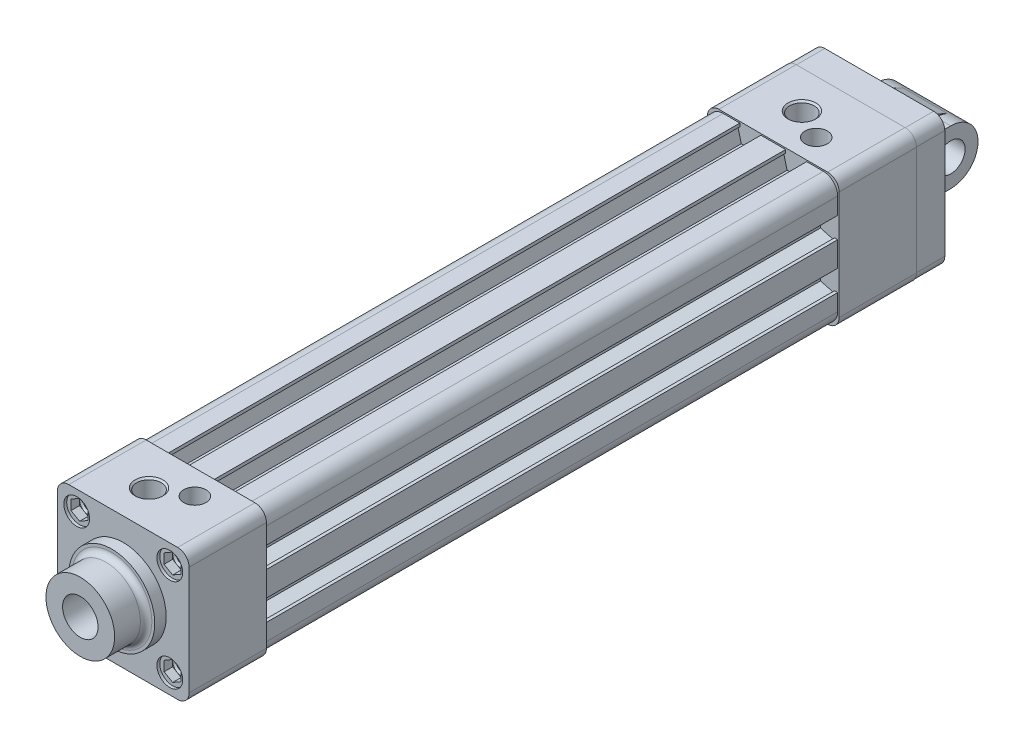
SolidWorks part; units mm, degrees
ref_plane "Front Plane" through (0, 0, 0) normal (0, 0, 1) x (1, 0, 0)
ref_plane "Top Plane" through (0, 0, 0) normal (0, 1, 0) x (1, 0, 0)
ref_plane "Right Plane" through (0, 0, 0) normal (1, 0, 0) x (0, 0, -1)
ref_plane "Plane1" through (0, 0, -254) normal (0, 0, 1) x (1, 0, 0)
sketch "Sketch1" plane through (0, 0, -254) normal (0, 0, 1) x (1, 0, 0)
  line L0 (-19, -23) -> (19, -23)
  line L1 (23, -19) -> (23, 19)
  line L2 (19, 23) -> (-19, 23)
  line L3 (-23, 19) -> (-23, -19)
  arc A0 (-23, -19) -> (-19, -23) centre (-19, -19) ccw
  arc A1 (19, -23) -> (23, -19) centre (19, -19) ccw
  arc A2 (23, 19) -> (19, 23) centre (19, 19) ccw
  arc A3 (-19, 23) -> (-23, 19) centre (-19, 19) ccw
extrude "Boss-Extrude1" add sketch "Sketch1" along normal blind 27
ref_plane "Plane2" through (0, 0, -227) normal (0, 0, 1) x (1, 0, 0)
sketch "Sketch2" plane through (0, 0, -227) normal (0, 0, 1) x (1, 0, 0)
  line L0 (-17.5, -22.5) -> (-11.675, -22.5)
  line L1 (-11.675, -22.5) -> (-11.675, -21.393)
  line L2 (-11.675, -21.393) -> (-12.3558, -21)
  line L3 (-12.3558, -21) -> (-11.15, -16.5)
  line L4 (-11.15, -16.5) -> (-4.85, -16.5)
  line L5 (-4.85, -16.5) -> (-3.6442, -21)
  line L6 (-3.6442, -21) -> (-4.325, -21.393)
  line L7 (-4.325, -21.393) -> (-4.325, -22.5)
  line L8 (-4.325, -22.5) -> (4.325, -22.5)
  line L9 (4.325, -22.5) -> (4.325, -21.393)
  line L10 (4.325, -21.393) -> (3.6442, -21)
  line L11 (3.6442, -21) -> (4.85, -16.5)
  line L12 (4.85, -16.5) -> (11.15, -16.5)
  line L13 (11.15, -16.5) -> (12.3558, -21)
  line L14 (12.3558, -21) -> (11.675, -21.393)
  line L15 (11.675, -21.393) -> (11.675, -22.5)
  line L16 (11.675, -22.5) -> (17.5, -22.5)
  line L17 (22.5, -17.5) -> (22.5, -11.675)
  line L18 (22.5, -11.675) -> (21.393, -11.675)
  line L19 (21.393, -11.675) -> (21, -12.3558)
  line L20 (21, -12.3558) -> (16.5, -11.15)
  line L21 (16.5, -11.15) -> (16.5, -4.85)
  line L22 (16.5, -4.85) -> (21, -3.6442)
  line L23 (21, -3.6442) -> (21.393, -4.325)
  line L24 (21.393, -4.325) -> (22.5, -4.325)
  line L25 (22.5, -4.325) -> (22.5, 4.325)
  line L26 (22.5, 4.325) -> (21.393, 4.325)
  line L27 (21.393, 4.325) -> (21, 3.6442)
  line L28 (21, 3.6442) -> (16.5, 4.85)
  line L29 (16.5, 4.85) -> (16.5, 11.15)
  line L30 (16.5, 11.15) -> (21, 12.3558)
  line L31 (21, 12.3558) -> (21.393, 11.675)
  line L32 (21.393, 11.675) -> (22.5, 11.675)
  line L33 (22.5, 11.675) -> (22.5, 17.5)
  line L34 (17.5, 22.5) -> (11.675, 22.5)
  line L35 (11.675, 22.5) -> (11.675, 21.393)
  line L36 (11.675, 21.393) -> (12.3558, 21)
  line L37 (12.3558, 21) -> (11.15, 16.5)
  line L38 (11.15, 16.5) -> (4.85, 16.5)
  line L39 (4.85, 16.5) -> (3.6442, 21)
  line L40 (3.6442, 21) -> (4.325, 21.393)
  line L41 (4.325, 21.393) -> (4.325, 22.5)
  line L42 (4.325, 22.5) -> (-4.325, 22.5)
  line L43 (-4.325, 22.5) -> (-4.325, 21.393)
  line L44 (-4.325, 21.393) -> (-3.6442, 21)
  line L45 (-3.6442, 21) -> (-4.85, 16.5)
  line L46 (-4.85, 16.5) -> (-11.15, 16.5)
  line L47 (-11.15, 16.5) -> (-12.3558, 21)
  line L48 (-12.3558, 21) -> (-11.675, 21.393)
  line L49 (-11.675, 21.393) -> (-11.675, 22.5)
  line L50 (-11.675, 22.5) -> (-17.5, 22.5)
  line L51 (-22.5, 17.5) -> (-22.5, 11.675)
  line L52 (-22.5, 11.675) -> (-21.393, 11.675)
  line L53 (-21.393, 11.675) -> (-21, 12.3558)
  line L54 (-21, 12.3558) -> (-16.5, 11.15)
  line L55 (-16.5, 11.15) -> (-16.5, 4.85)
  line L56 (-16.5, 4.85) -> (-21, 3.6442)
  line L57 (-21, 3.6442) -> (-21.393, 4.325)
  line L58 (-21.393, 4.325) -> (-22.5, 4.325)
  line L59 (-22.5, 4.325) -> (-22.5, -4.325)
  line L60 (-22.5, -4.325) -> (-21.393, -4.325)
  line L61 (-21.393, -4.325) -> (-21, -3.6442)
  line L62 (-21, -3.6442) -> (-16.5, -4.85)
  line L63 (-16.5, -4.85) -> (-16.5, -11.15)
  line L64 (-16.5, -11.15) -> (-21, -12.3558)
  line L65 (-21, -12.3558) -> (-21.393, -11.675)
  line L66 (-21.393, -11.675) -> (-22.5, -11.675)
  line L67 (-22.5, -11.675) -> (-22.5, -17.5)
  arc A0 (-22.5, -17.5) -> (-17.5, -22.5) centre (-17.5, -17.5) ccw
  arc A1 (17.5, -22.5) -> (22.5, -17.5) centre (17.5, -17.5) ccw
  arc A2 (22.5, 17.5) -> (17.5, 22.5) centre (17.5, 17.5) ccw
  arc A3 (-17.5, 22.5) -> (-22.5, 17.5) centre (-17.5, 17.5) ccw
extrude "Boss-Extrude2" add sketch "Sketch2" along normal blind 200
ref_plane "Plane3" through (0, 0, 0) normal (0, 0, 1) x (1, 0, 0)
sketch "Sketch3" plane through (0, 0, 0) normal (0, 0, 1) x (1, 0, 0)
  line L0 (-19, -23) -> (19, -23)
  line L1 (23, -19) -> (23, 19)
  line L2 (19, 23) -> (-19, 23)
  line L3 (-23, 19) -> (-23, -19)
  arc A0 (-23, -19) -> (-19, -23) centre (-19, -19) ccw
  arc A1 (19, -23) -> (23, -19) centre (19, -19) ccw
  arc A2 (23, 19) -> (19, 23) centre (19, 19) ccw
  arc A3 (-19, 23) -> (-23, 19) centre (-19, 19) ccw
extrude "Boss-Extrude3" add sketch "Sketch3" against normal blind 27
ref_plane "Plane4" through (0, 0, 0) normal (0, 0, 1) x (1, 0, 0)
sketch "Sketch4" plane through (0, 0, 0) normal (0, 0, 1) x (1, 0, 0)
  line L0 (13.25, 17.9821) -> (13.25, 14.5179)
  line L1 (13.25, 14.5179) -> (16.25, 12.7859)
  line L2 (16.25, 12.7859) -> (19.25, 14.5179)
  line L3 (19.25, 14.5179) -> (19.25, 17.9821)
  line L4 (19.25, 17.9821) -> (16.25, 19.7141)
  line L5 (16.25, 19.7141) -> (13.25, 17.9821)
extrude "Cut-Extrude1" cut sketch "Sketch4" against normal blind 4
ref_plane "Plane5" through (16.25, 0, 0) normal (1, 0, 0) x (0, 0, -1)
sketch "Sketch5" plane through (16.25, 0, 0) normal (1, 0, 0) x (0, 0, -1)
  line L0 (17, 16.25) -> (17, 13.8635)
  line L1 (17, 13.8635) -> (4.6135, 13.8635)
  line L2 (4.6135, 13.8635) -> (4, 13.25)
  line L3 (4, 13.25) -> (1, 13.25)
  line L4 (1, 13.25) -> (1, 11.75)
  line L5 (1, 11.75) -> (-1, 11.75)
  line L6 (-1, 11.75) -> (-1, 16.25)
  line L7 (-1, 16.25) -> (17, 16.25)
  line L8 (-1, 16.25) -> (17, 16.25) construction
revolve "Cut-Revolve1" cut sketch "Sketch5" angle 360 about L8
cosmetic thread "Cosmetic Thread1" parameters "D1"=12.3865, "D2"=6
ref_plane "Plane6" through (0, 0, 0) normal (0, 0, 1) x (1, 0, 0)
sketch "Sketch6" plane through (0, 0, 0) normal (0, 0, 1) x (1, 0, 0)
  line L0 (-19.25, 17.9821) -> (-19.25, 14.5179)
  line L1 (-19.25, 14.5179) -> (-16.25, 12.7859)
  line L2 (-16.25, 12.7859) -> (-13.25, 14.5179)
  line L3 (-13.25, 14.5179) -> (-13.25, 17.9821)
  line L4 (-13.25, 17.9821) -> (-16.25, 19.7141)
  line L5 (-16.25, 19.7141) -> (-19.25, 17.9821)
extrude "Cut-Extrude2" cut sketch "Sketch6" against normal blind 4
ref_plane "Plane7" through (-16.25, 0, 0) normal (1, 0, 0) x (0, 0, -1)
sketch "Sketch7" plane through (-16.25, 0, 0) normal (1, 0, 0) x (0, 0, -1)
  line L0 (17, 16.25) -> (17, 13.8635)
  line L1 (17, 13.8635) -> (4.6135, 13.8635)
  line L2 (4.6135, 13.8635) -> (4, 13.25)
  line L3 (4, 13.25) -> (1, 13.25)
  line L4 (1, 13.25) -> (1, 11.75)
  line L5 (1, 11.75) -> (-1, 11.75)
  line L6 (-1, 11.75) -> (-1, 16.25)
  line L7 (-1, 16.25) -> (17, 16.25)
  line L8 (-1, 16.25) -> (17, 16.25) construction
revolve "Cut-Revolve2" cut sketch "Sketch7" angle 360 about L8
cosmetic thread "Cosmetic Thread2" parameters "D1"=12.3865, "D2"=6
ref_plane "Plane8" through (0, 0, 0) normal (0, 0, 1) x (1, 0, 0)
sketch "Sketch8" plane through (0, 0, 0) normal (0, 0, 1) x (1, 0, 0)
  line L0 (-19.25, -17.9821) -> (-16.25, -19.7141)
  line L1 (-16.25, -19.7141) -> (-13.25, -17.9821)
  line L2 (-13.25, -17.9821) -> (-13.25, -14.5179)
  line L3 (-13.25, -14.5179) -> (-16.25, -12.7859)
  line L4 (-16.25, -12.7859) -> (-19.25, -14.5179)
  line L5 (-19.25, -14.5179) -> (-19.25, -17.9821)
extrude "Cut-Extrude3" cut sketch "Sketch8" against normal blind 4
ref_plane "Plane9" through (-16.25, 0, 0) normal (1, 0, 0) x (0, 0, -1)
sketch "Sketch9" plane through (-16.25, 0, 0) normal (1, 0, 0) x (0, 0, -1)
  line L0 (-1, -16.25) -> (-1, -11.75)
  line L1 (-1, -11.75) -> (1, -11.75)
  line L2 (1, -11.75) -> (1, -13.25)
  line L3 (1, -13.25) -> (4, -13.25)
  line L4 (4, -13.25) -> (4.6135, -13.8635)
  line L5 (4.6135, -13.8635) -> (17, -13.8635)
  line L6 (17, -13.8635) -> (17, -16.25)
  line L7 (17, -16.25) -> (-1, -16.25)
  line L8 (17, -16.25) -> (-1, -16.25) construction
revolve "Cut-Revolve3" cut sketch "Sketch9" angle 360 about L8
cosmetic thread "Cosmetic Thread3" parameters "D1"=12.3865, "D2"=6
ref_plane "Plane10" through (0, 0, 0) normal (0, 0, 1) x (1, 0, 0)
sketch "Sketch10" plane through (0, 0, 0) normal (0, 0, 1) x (1, 0, 0)
  line L0 (13.25, -14.5179) -> (13.25, -17.9821)
  line L1 (13.25, -17.9821) -> (16.25, -19.7141)
  line L2 (16.25, -19.7141) -> (19.25, -17.9821)
  line L3 (19.25, -17.9821) -> (19.25, -14.5179)
  line L4 (19.25, -14.5179) -> (16.25, -12.7859)
  line L5 (16.25, -12.7859) -> (13.25, -14.5179)
extrude "Cut-Extrude4" cut sketch "Sketch10" against normal blind 4
ref_plane "Plane11" through (16.25, 0, 0) normal (1, 0, 0) x (0, 0, -1)
sketch "Sketch11" plane through (16.25, 0, 0) normal (1, 0, 0) x (0, 0, -1)
  line L0 (-1, -16.25) -> (-1, -11.75)
  line L1 (-1, -11.75) -> (1, -11.75)
  line L2 (1, -11.75) -> (1, -13.25)
  line L3 (1, -13.25) -> (4, -13.25)
  line L4 (4, -13.25) -> (4.6135, -13.8635)
  line L5 (4.6135, -13.8635) -> (17, -13.8635)
  line L6 (17, -13.8635) -> (17, -16.25)
  line L7 (17, -16.25) -> (-1, -16.25)
  line L8 (17, -16.25) -> (-1, -16.25) construction
revolve "Cut-Revolve4" cut sketch "Sketch11" angle 360 about L8
cosmetic thread "Cosmetic Thread4" parameters "D1"=12.3865, "D2"=6
ref_plane "Plane12" through (0, 0, -254) normal (0, 0, 1) x (1, 0, 0)
sketch "Sketch12" plane through (0, 0, -254) normal (0, 0, 1) x (1, 0, 0)
  line L0 (13.25, 17.9821) -> (13.25, 14.5179)
  line L1 (13.25, 14.5179) -> (16.25, 12.7859)
  line L2 (16.25, 12.7859) -> (19.25, 14.5179)
  line L3 (19.25, 14.5179) -> (19.25, 17.9821)
  line L4 (19.25, 17.9821) -> (16.25, 19.7141)
  line L5 (16.25, 19.7141) -> (13.25, 17.9821)
extrude "Cut-Extrude5" cut sketch "Sketch12" along normal blind 4
ref_plane "Plane13" through (16.25, 0, 0) normal (1, 0, 0) x (0, 0, -1)
sketch "Sketch13" plane through (16.25, 0, 0) normal (1, 0, 0) x (0, 0, -1)
  line L0 (255, 16.25) -> (255, 11.75)
  line L1 (255, 11.75) -> (253, 11.75)
  line L2 (253, 11.75) -> (253, 13.25)
  line L3 (253, 13.25) -> (250, 13.25)
  line L4 (250, 13.25) -> (249.3865, 13.8635)
  line L5 (249.3865, 13.8635) -> (237, 13.8635)
  line L6 (237, 13.8635) -> (237, 16.25)
  line L7 (237, 16.25) -> (255, 16.25)
  line L8 (237, 16.25) -> (255, 16.25) construction
revolve "Cut-Revolve5" cut sketch "Sketch13" angle 360 about L8
cosmetic thread "Cosmetic Thread5" parameters "D1"=12.3865, "D2"=6
ref_plane "Plane14" through (0, 0, -254) normal (0, 0, 1) x (1, 0, 0)
sketch "Sketch14" plane through (0, 0, -254) normal (0, 0, 1) x (1, 0, 0)
  line L0 (-19.25, 17.9821) -> (-19.25, 14.5179)
  line L1 (-19.25, 14.5179) -> (-16.25, 12.7859)
  line L2 (-16.25, 12.7859) -> (-13.25, 14.5179)
  line L3 (-13.25, 14.5179) -> (-13.25, 17.9821)
  line L4 (-13.25, 17.9821) -> (-16.25, 19.7141)
  line L5 (-16.25, 19.7141) -> (-19.25, 17.9821)
extrude "Cut-Extrude6" cut sketch "Sketch14" along normal blind 4
ref_plane "Plane15" through (-16.25, 0, 0) normal (1, 0, 0) x (0, 0, -1)
sketch "Sketch15" plane through (-16.25, 0, 0) normal (1, 0, 0) x (0, 0, -1)
  line L0 (255, 16.25) -> (255, 11.75)
  line L1 (255, 11.75) -> (253, 11.75)
  line L2 (253, 11.75) -> (253, 13.25)
  line L3 (253, 13.25) -> (250, 13.25)
  line L4 (250, 13.25) -> (249.3865, 13.8635)
  line L5 (249.3865, 13.8635) -> (237, 13.8635)
  line L6 (237, 13.8635) -> (237, 16.25)
  line L7 (237, 16.25) -> (255, 16.25)
  line L8 (237, 16.25) -> (255, 16.25) construction
revolve "Cut-Revolve6" cut sketch "Sketch15" angle 360 about L8
cosmetic thread "Cosmetic Thread6" parameters "D1"=12.3865, "D2"=6
ref_plane "Plane16" through (0, 0, -254) normal (0, 0, 1) x (1, 0, 0)
sketch "Sketch16" plane through (0, 0, -254) normal (0, 0, 1) x (1, 0, 0)
  line L0 (13.25, -14.5179) -> (13.25, -17.9821)
  line L1 (13.25, -17.9821) -> (16.25, -19.7141)
  line L2 (16.25, -19.7141) -> (19.25, -17.9821)
  line L3 (19.25, -17.9821) -> (19.25, -14.5179)
  line L4 (19.25, -14.5179) -> (16.25, -12.7859)
  line L5 (16.25, -12.7859) -> (13.25, -14.5179)
extrude "Cut-Extrude7" cut sketch "Sketch16" along normal blind 4
ref_plane "Plane17" through (16.25, 0, 0) normal (1, 0, 0) x (0, 0, -1)
sketch "Sketch17" plane through (16.25, 0, 0) normal (1, 0, 0) x (0, 0, -1)
  line L0 (237, -16.25) -> (237, -13.8635)
  line L1 (237, -13.8635) -> (249.3865, -13.8635)
  line L2 (249.3865, -13.8635) -> (250, -13.25)
  line L3 (250, -13.25) -> (253, -13.25)
  line L4 (253, -13.25) -> (253, -11.75)
  line L5 (253, -11.75) -> (255, -11.75)
  line L6 (255, -11.75) -> (255, -16.25)
  line L7 (255, -16.25) -> (237, -16.25)
  line L8 (255, -16.25) -> (237, -16.25) construction
revolve "Cut-Revolve7" cut sketch "Sketch17" angle 360 about L8
cosmetic thread "Cosmetic Thread7" parameters "D1"=12.3865, "D2"=6
ref_plane "Plane18" through (0, 0, -254) normal (0, 0, 1) x (1, 0, 0)
sketch "Sketch18" plane through (0, 0, -254) normal (0, 0, 1) x (1, 0, 0)
  line L0 (-19.25, -14.5179) -> (-19.25, -17.9821)
  line L1 (-19.25, -17.9821) -> (-16.25, -19.7141)
  line L2 (-16.25, -19.7141) -> (-13.25, -17.9821)
  line L3 (-13.25, -17.9821) -> (-13.25, -14.5179)
  line L4 (-13.25, -14.5179) -> (-16.25, -12.7859)
  line L5 (-16.25, -12.7859) -> (-19.25, -14.5179)
extrude "Cut-Extrude8" cut sketch "Sketch18" along normal blind 4
ref_plane "Plane19" through (-16.25, 0, 0) normal (1, 0, 0) x (0, 0, -1)
sketch "Sketch19" plane through (-16.25, 0, 0) normal (1, 0, 0) x (0, 0, -1)
  line L0 (237, -16.25) -> (237, -13.8635)
  line L1 (237, -13.8635) -> (249.3865, -13.8635)
  line L2 (249.3865, -13.8635) -> (250, -13.25)
  line L3 (250, -13.25) -> (253, -13.25)
  line L4 (253, -13.25) -> (253, -11.75)
  line L5 (253, -11.75) -> (255, -11.75)
  line L6 (255, -11.75) -> (255, -16.25)
  line L7 (255, -16.25) -> (237, -16.25)
  line L8 (255, -16.25) -> (237, -16.25) construction
revolve "Cut-Revolve8" cut sketch "Sketch19" angle 360 about L8
cosmetic thread "Cosmetic Thread8" parameters "D1"=12.3865, "D2"=6
ref_plane "Plane20" through (-4, 0, 0) normal (1, 0, 0) x (0, 0, -1)
sketch "Sketch20" plane through (-4, 0, 0) normal (1, 0, 0) x (0, 0, -1)
  line L0 (13, 23) -> (17.864, 23)
  line L1 (17.864, 23) -> (17.283, 22.419)
  line L2 (17.283, 22.419) -> (17.283, 10.2928)
  line L3 (17.283, 10.2928) -> (13, 7.82)
  line L4 (13, 7.82) -> (13, 23)
  line L5 (13, -50) -> (13, 23) construction
revolve "Cut-Revolve9" cut sketch "Sketch20" angle 360 about L5
cosmetic thread "Cosmetic Thread9" parameters "D1"=11.5, "D2"=9.728
ref_plane "Plane21" through (6.5, 0, 0) normal (1, 0, 0) x (0, 0, -1)
sketch "Sketch21" plane through (6.5, 0, 0) normal (1, 0, 0) x (0, 0, -1)
  line L0 (18.5, 23) -> (22.4, 23)
  line L1 (22.4, 23) -> (22.4, 16.25)
  line L2 (22.4, 16.25) -> (18.5, 16.25)
  line L3 (18.5, 16.25) -> (18.5, 23)
  line L4 (18.5, 16.25) -> (18.5, 23) construction
revolve "Cut-Revolve10" cut sketch "Sketch21" angle 360 about L4
ref_plane "Plane22" through (0, 16.25, 0) normal (0, 1, 0) x (-1, 0, 0)
sketch "Sketch22" plane through (0, 16.25, 0) normal (0, 1, 0) x (-1, 0, 0)
  line L0 (-5.7783, -17.25) -> (-7.2217, -17.25)
  line L1 (-7.2217, -17.25) -> (-7.9434, -18.5)
  line L2 (-7.9434, -18.5) -> (-7.2217, -19.75)
  line L3 (-7.2217, -19.75) -> (-5.7783, -19.75)
  line L4 (-5.7783, -19.75) -> (-5.0566, -18.5)
  line L5 (-5.0566, -18.5) -> (-5.7783, -17.25)
extrude "Cut-Extrude9" cut sketch "Sketch22" against normal blind 2.5
ref_plane "Plane23" through (-4, 0, 0) normal (1, 0, 0) x (0, 0, -1)
sketch "Sketch23" plane through (-4, 0, 0) normal (1, 0, 0) x (0, 0, -1)
  line L0 (241, 23) -> (245.864, 23)
  line L1 (245.864, 23) -> (245.283, 22.419)
  line L2 (245.283, 22.419) -> (245.283, 10.2928)
  line L3 (245.283, 10.2928) -> (241, 7.82)
  line L4 (241, 7.82) -> (241, 23)
  line L5 (241, -50) -> (241, 23) construction
revolve "Cut-Revolve11" cut sketch "Sketch23" angle 360 about L5
cosmetic thread "Cosmetic Thread10" parameters "D1"=11.5, "D2"=9.728
ref_plane "Plane24" through (6.5, 0, 0) normal (1, 0, 0) x (0, 0, -1)
sketch "Sketch24" plane through (6.5, 0, 0) normal (1, 0, 0) x (0, 0, -1)
  line L0 (235.5, 23) -> (239.4, 23)
  line L1 (239.4, 23) -> (239.4, 16.25)
  line L2 (239.4, 16.25) -> (235.5, 16.25)
  line L3 (235.5, 16.25) -> (235.5, 23)
  line L4 (235.5, 16.25) -> (235.5, 23) construction
revolve "Cut-Revolve12" cut sketch "Sketch24" angle 360 about L4
ref_plane "Plane25" through (0, 0, -254) normal (0, 0, 1) x (1, 0, 0)
sketch "Sketch25" plane through (0, 0, -254) normal (0, 0, 1) x (1, 0, 0)
  line L0 (-19, -22.9) -> (19, -22.9)
  line L1 (22.9, -19) -> (22.9, 19)
  line L2 (19, 22.9) -> (-19, 22.9)
  line L3 (-22.9, 19) -> (-22.9, -19)
  arc A0 (-22.9, -19) -> (-19, -22.9) centre (-19, -19) ccw
  arc A1 (19, -22.9) -> (22.9, -19) centre (19, -19) ccw
  arc A2 (22.9, 19) -> (19, 22.9) centre (19, 19) ccw
  arc A3 (-19, 22.9) -> (-22.9, 19) centre (-19, 19) ccw
extrude "Boss-Extrude4" add sketch "Sketch25" against normal blind 10
ref_plane "Plane26" through (0, 0, 0) normal (1, 0, 0) x (0, 0, -1)
sketch "Sketch26" plane through (0, 0, 0) normal (1, 0, 0) x (0, 0, -1)
  line L0 (264, -16.1) -> (280.0247, -8.6053)
  line L1 (280.0247, 8.6053) -> (264, 16.1)
  line L2 (264, 16.1) -> (264, -16.1)
  arc A0 (280.0247, -8.6053) -> (280.0247, 8.6053) centre (276, 0) ccw
extrude "Boss-Extrude5" add sketch "Sketch26" against normal blind 7.8 and the other way blind 7.8
ref_plane "Plane27" through (0, 0, 0) normal (1, 0, 0) x (0, 0, -1)
sketch "Sketch27" plane through (0, 0, 0) normal (1, 0, 0) x (0, 0, -1)
  line L0 (263, -9.5) -> (276, -9.5)
  line L1 (276, 9.5) -> (263, 9.5)
  line L2 (263, 9.5) -> (263, -9.5)
  arc A0 (276, -9.5) -> (276, 9.5) centre (276, 0) ccw
extrude "Boss-Extrude6" add sketch "Sketch27" against normal blind 13 and the other way blind 13
ref_plane "Plane28" through (0, 0, 0) normal (1, 0, 0) x (0, 0, -1)
sketch "Sketch28" plane through (0, 0, 0) normal (1, 0, 0) x (0, 0, -1)
  circle A0 centre (276, 0) radius 5
extrude "Cut-Extrude10" cut sketch "Sketch28" against normal blind 14 and the other way blind 14
ref_plane "Plane29" through (0, 0, 0) normal (1, 0, 0) x (0, 0, -1)
sketch "Sketch29" plane through (0, 0, 0) normal (1, 0, 0) x (0, 0, -1)
  line L0 (-15, 0) -> (-15, 12)
  line L1 (-15, 12) -> (-6, 12)
  line L2 (-4, 14) -> (-4, 15)
  line L3 (-4, 15) -> (0, 15)
  line L4 (0, 15) -> (0, 0)
  line L5 (0, 0) -> (-15, 0)
  line L6 (0, 0) -> (-15, 0) construction
  arc A0 (-6, 12) -> (-4, 14) centre (-6, 14) ccw
revolve "Revolve1" add sketch "Sketch29" angle 360 about L6
ref_plane "Plane30" through (0, 0, 15) normal (0, 0, 1) x (1, 0, 0)
sketch "Sketch30" plane through (0, 0, 15) normal (0, 0, 1) x (1, 0, 0)
  circle A0 centre (0, 0) radius 6.2
extrude "Cut-Extrude11" cut sketch "Sketch30" against normal blind 162
